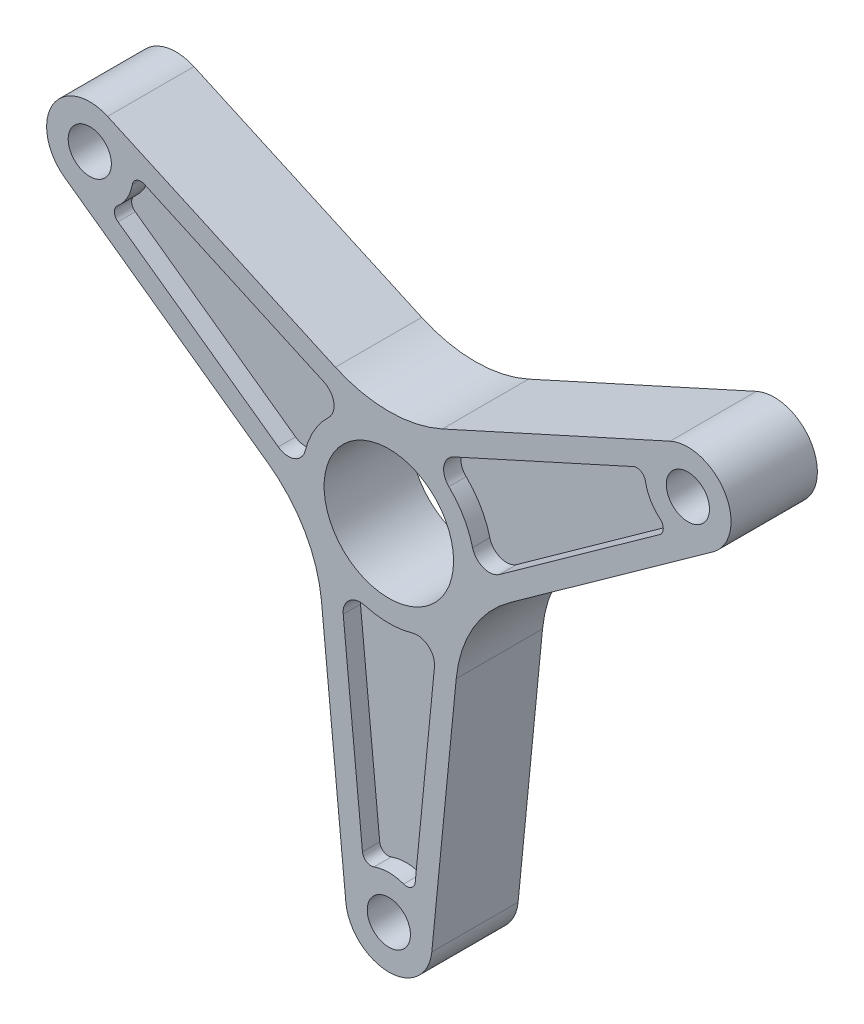
SolidWorks part; units mm, degrees
ref_plane "Front Plane" through (0, 0, 0) normal (0, 0, 1) x (1, 0, 0)
ref_plane "Top Plane" through (0, 0, 0) normal (0, 1, 0) x (1, 0, 0)
ref_plane "Right Plane" through (0, 0, 0) normal (1, 0, 0) x (0, 0, -1)
sketch "Sketch1" plane through (0, 0, 0) normal (0, 0, 1) x (1, 0, 0)
  line L0 (0, 0) -> (0, -80) construction
  line L1 (-9.9522, -80.9766) -> (-15.6097, -23.3203)
  line L2 (9.9522, -80.9766) -> (15.6097, -23.3203)
  line L3 (-75.1039, 31.8694) -> (-28.0009, -1.8583)
  line L4 (-65.1517, 49.1071) -> (-12.3911, 25.1786)
  line L5 (65.1517, 49.1071) -> (12.3911, 25.1786)
  line L6 (75.1039, 31.8694) -> (28.0009, -1.8583)
  circle A0 centre (0, 0) radius 15
  circle A1 centre (0, 0) radius 22.5 construction
  circle A2 centre (0, -80) radius 5
  arc A3 (-9.9522, -80.9766) -> (9.9522, -80.9766) centre (0, -80) ccw
  arc A4 (-65.1517, 49.1071) -> (-75.1039, 31.8694) centre (-69.282, 40) ccw
  circle A5 centre (-69.282, 40) radius 5
  arc A6 (75.1039, 31.8694) -> (65.1517, 49.1071) centre (69.282, 40) ccw
  circle A7 centre (69.282, 40) radius 5
  arc A8 (-12.3911, 25.1786) -> (12.3911, 25.1786) centre (0, 52.5) ccw
  arc A9 (15.6097, -23.3203) -> (28.0009, -1.8583) centre (45.4663, -26.25) cw
  arc A10 (-28.0009, -1.8583) -> (-15.6097, -23.3203) centre (-45.4663, -26.25) cw
  dimension "D1" = 30
  dimension "D2" = 45
  dimension "D3" = 80
  dimension "D4" = 10
  dimension "D5" = 20
  dimension "D7" = 30
  dimension "D8" = 30
  dimension "D6" = 3
extrude "Boss-Extrude2" add sketch "Sketch1" along normal blind 20
sketch "Sketch3" plane through (0, 0, 0) normal (0, 0, -1) x (-1, 0, 0)
  line L0 (0, 0) -> (0, -80) construction
  line L1 (10.5712, -23.468) -> (6.1108, -68.9249)
  line L2 (15.6097, -23.3203) -> (9.9522, -80.9766) construction
  line L3 (-10.5712, -23.468) -> (-6.1108, -68.9249)
  line L4 (-25.6095, 2.5791) -> (-62.7461, 29.1704)
  line L5 (-15.0383, 20.889) -> (-56.6353, 39.7545)
  line L6 (15.0383, 20.889) -> (56.6353, 39.7545)
  line L7 (25.6095, 2.5791) -> (62.7461, 29.1704)
  arc A0 (3.4336, -70.608) -> (-3.4336, -70.608) centre (0, -80) ccw
  arc A1 (-5.4919, -19.2312) -> (5.4919, -19.2312) centre (0, 0) ccw
  arc A2 (10.5712, -23.468) -> (5.4919, -19.2312) centre (6.5903, -23.0774) ccw
  arc A3 (-10.5712, -23.468) -> (-5.4919, -19.2312) centre (-6.5903, -23.0774) cw
  arc A4 (-6.1108, -68.9249) -> (-3.4336, -70.608) centre (-4.1203, -68.7296) ccw
  arc A5 (6.1108, -68.9249) -> (3.4336, -70.608) centre (4.1203, -68.7296) cw
  arc A6 (-25.6095, 2.5791) -> (-19.4007, 4.8594) centre (-23.2808, 5.8313) ccw
  arc A7 (-13.9087, 14.3718) -> (-19.4007, 4.8594) centre (0, 0) ccw
  arc A8 (-15.0383, 20.889) -> (-13.9087, 14.3718) centre (-16.6905, 17.2461) cw
  arc A9 (-62.8651, 32.3304) -> (-59.4315, 38.2776) centre (-69.282, 40) ccw
  arc A10 (-62.7461, 29.1704) -> (-62.8651, 32.3304) centre (-61.5817, 30.7965) cw
  arc A11 (-56.6353, 39.7545) -> (-59.4315, 38.2776) centre (-57.4614, 37.9331) ccw
  arc A12 (15.0383, 20.889) -> (13.9087, 14.3718) centre (16.6905, 17.2461) ccw
  arc A13 (19.4007, 4.8594) -> (13.9087, 14.3718) centre (0, 0) ccw
  arc A14 (25.6095, 2.5791) -> (19.4007, 4.8594) centre (23.2808, 5.8313) cw
  arc A15 (59.4315, 38.2776) -> (62.8651, 32.3304) centre (69.282, 40) ccw
  arc A16 (56.6353, 39.7545) -> (59.4315, 38.2776) centre (57.4614, 37.9331) cw
  arc A17 (62.7461, 29.1704) -> (62.8651, 32.3304) centre (61.5817, 30.7965) ccw
  point P9 (11.2515, -16.5349)
  point P17 (-11.2515, -16.5349)
  point P20 (-5.8218, -71.8694)
  point P23 (5.8218, -71.8694)
  dimension "D1" = 20
  dimension "D2" = 40
  dimension "D4" = 4
  dimension "D5" = 2
  dimension "D3" = 5
  dimension "D6" = 3
sketch "Sketch7" plane through (0, 0, 20) normal (0, 0, 1) x (1, 0, 0)
  line L0 (-25.6095, 2.5791) -> (-62.7461, 29.1704) construction
  line L1 (-15.0383, 20.889) -> (-56.6353, 39.7545) construction
  line L2 (-25.6095, 2.5791) -> (-62.7461, 29.1704)
  line L3 (-15.0383, 20.889) -> (-56.6353, 39.7545)
  line L4 (25.6095, 2.5791) -> (62.7461, 29.1704)
  line L5 (15.0383, 20.889) -> (56.6353, 39.7545)
  line L6 (-15.6097, -23.3203) -> (-9.9522, -80.9766)
  line L7 (9.9522, -80.9766) -> (15.6097, -23.3203)
  line L8 (28.0009, -1.8583) -> (75.1039, 31.8694)
  line L9 (65.1517, 49.1071) -> (12.3911, 25.1786)
  line L10 (-12.3911, 25.1786) -> (-65.1517, 49.1071)
  line L11 (-75.1039, 31.8694) -> (-28.0009, -1.8583)
  line L12 (-15.6097, -23.3203) -> (-9.9522, -80.9766)
  line L13 (9.9522, -80.9766) -> (15.6097, -23.3203)
  line L14 (28.0009, -1.8583) -> (75.1039, 31.8694)
  line L15 (65.1517, 49.1071) -> (12.3911, 25.1786)
  line L16 (-12.3911, 25.1786) -> (-65.1517, 49.1071)
  line L17 (-75.1039, 31.8694) -> (-28.0009, -1.8583)
  line L18 (-10.5712, -23.468) -> (-6.1108, -68.9249)
  line L19 (10.5712, -23.468) -> (6.1108, -68.9249)
  arc A0 (-62.8651, 32.3304) -> (-62.7461, 29.1704) centre (-61.5817, 30.7965) ccw construction
  arc A1 (-56.6353, 39.7545) -> (-59.4315, 38.2776) centre (-57.4614, 37.9331) ccw construction
  arc A2 (-62.8651, 32.3304) -> (-59.4315, 38.2776) centre (-69.282, 40) ccw construction
  arc A3 (-25.6095, 2.5791) -> (-19.4007, 4.8594) centre (-23.2808, 5.8313) ccw construction
  arc A4 (-13.9087, 14.3718) -> (-19.4007, 4.8594) centre (0, 0) ccw construction
  arc A5 (-13.9087, 14.3718) -> (-15.0383, 20.889) centre (-16.6905, 17.2461) ccw construction
  arc A6 (-15.6097, -23.3203) -> (-28.0009, -1.8583) centre (-45.4663, -26.25) ccw
  arc A7 (-9.9522, -80.9766) -> (9.9522, -80.9766) centre (0, -80) ccw
  arc A8 (28.0009, -1.8583) -> (15.6097, -23.3203) centre (45.4663, -26.25) ccw
  arc A9 (75.1039, 31.8694) -> (65.1517, 49.1071) centre (69.282, 40) ccw
  arc A10 (-12.3911, 25.1786) -> (12.3911, 25.1786) centre (0, 52.5) ccw
  arc A11 (-65.1517, 49.1071) -> (-75.1039, 31.8694) centre (-69.282, 40) ccw
  arc A12 (-15.6097, -23.3203) -> (-28.0009, -1.8583) centre (-45.4663, -26.25) ccw
  arc A13 (-9.9522, -80.9766) -> (9.9522, -80.9766) centre (0, -80) ccw
  arc A14 (28.0009, -1.8583) -> (15.6097, -23.3203) centre (45.4663, -26.25) ccw
  arc A15 (75.1039, 31.8694) -> (65.1517, 49.1071) centre (69.282, 40) ccw
  arc A16 (-12.3911, 25.1786) -> (12.3911, 25.1786) centre (0, 52.5) ccw
  arc A17 (-65.1517, 49.1071) -> (-75.1039, 31.8694) centre (-69.282, 40) ccw
  arc A18 (-62.8651, 32.3304) -> (-62.7461, 29.1704) centre (-61.5817, 30.7965) ccw
  arc A19 (-56.6353, 39.7545) -> (-59.4315, 38.2776) centre (-57.4614, 37.9331) ccw
  arc A20 (-62.8651, 32.3304) -> (-59.4315, 38.2776) centre (-69.282, 40) ccw
  arc A21 (-25.6095, 2.5791) -> (-19.4007, 4.8594) centre (-23.2808, 5.8313) ccw
  arc A22 (-13.9087, 14.3718) -> (-19.4007, 4.8594) centre (0, 0) ccw
  arc A23 (-13.9087, 14.3718) -> (-15.0383, 20.889) centre (-16.6905, 17.2461) ccw
  arc A24 (19.4007, 4.8594) -> (25.6095, 2.5791) centre (23.2808, 5.8313) ccw
  arc A25 (19.4007, 4.8594) -> (13.9087, 14.3718) centre (0, 0) ccw
  arc A26 (15.0383, 20.889) -> (13.9087, 14.3718) centre (16.6905, 17.2461) ccw
  arc A27 (59.4315, 38.2776) -> (62.8651, 32.3304) centre (69.282, 40) ccw
  arc A28 (62.7461, 29.1704) -> (62.8651, 32.3304) centre (61.5817, 30.7965) ccw
  arc A29 (59.4315, 38.2776) -> (56.6353, 39.7545) centre (57.4614, 37.9331) ccw
  arc A30 (-5.4919, -19.2312) -> (-10.5712, -23.468) centre (-6.5903, -23.0774) ccw
  arc A31 (-5.4919, -19.2312) -> (5.4919, -19.2312) centre (0, 0) ccw
  arc A32 (10.5712, -23.468) -> (5.4919, -19.2312) centre (6.5903, -23.0774) ccw
  arc A33 (3.4336, -70.608) -> (-3.4336, -70.608) centre (0, -80) ccw
  arc A34 (-6.1108, -68.9249) -> (-3.4336, -70.608) centre (-4.1203, -68.7296) ccw
  arc A35 (3.4336, -70.608) -> (6.1108, -68.9249) centre (4.1203, -68.7296) ccw
  dimension "D1" = 0
  dimension "D2" = 3
extrude "Cut-Extrude4" cut sketch "Sketch7" against normal blind 4 flip side to cut
extrude "Cut-Extrude5" cut sketch "Sketch3" against normal blind 4
